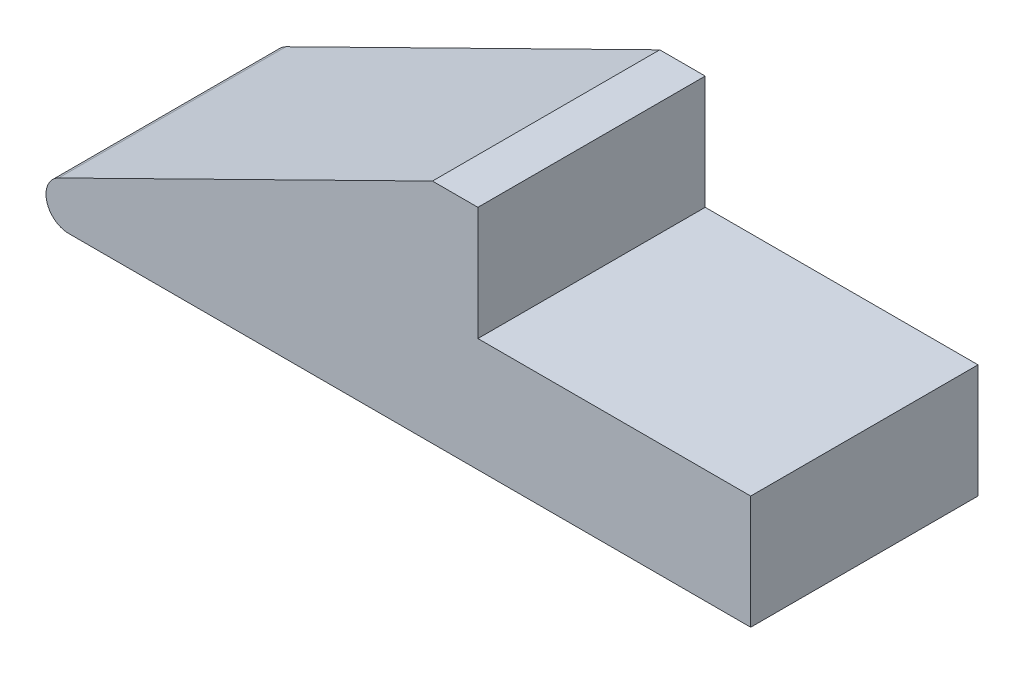
SolidWorks part; units mm, degrees
material "2024 Alloy"
ref_plane "Plane1" through (0, 0, 0) normal (0, 0, 1) x (1, 0, 0)
ref_plane "Plane2" through (0, 0, 0) normal (0, 1, 0) x (1, 0, 0)
ref_plane "Plane3" through (0, 0, 0) normal (1, 0, 0) x (0, 0, -1)
sketch "Sketch1" plane through (0, 0, 0) normal (0, 0, 1) x (1, 0, 0)
  line L0 (-0.4421, 1.897) -> (16, 10)
  line L1 (18, 10) -> (18, 5)
  line L2 (30, 0) -> (0, 0)
  line L3 (30, 0) -> (30, 5)
  line L4 (30, 5) -> (18, 5)
  line L5 (0, -50) -> (0, 50) construction
  line L6 (50, 0) -> (-50, 0) construction
  line L7 (18, 10) -> (16, 10)
  arc A0 (0, 0) -> (-0.4421, 1.897) centre (0, 1) cw
  dimension "D1" = 1
  dimension "D2" = 5
  dimension "D3" = 5
  dimension "D4" = 30
  dimension "D5" = 12
  dimension "D6" = 2
extrude "Base-Extrude" add sketch "Sketch1" along normal mid plane 10
